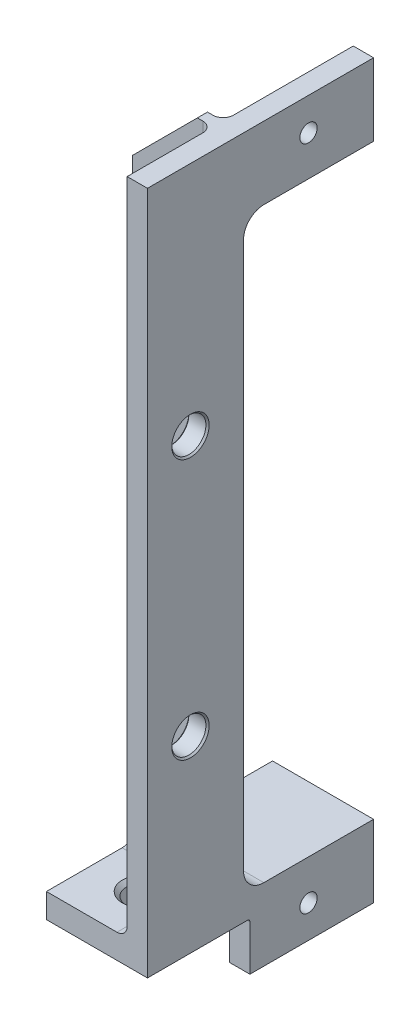
SolidWorks part; units mm, degrees
material "6061-T6 (SS)"
ref_plane "Front Plane" through (0, 0, 0) normal (0, 0, 1) x (1, 0, 0)
ref_plane "Top Plane" through (0, 0, 0) normal (0, 1, 0) x (1, 0, 0)
ref_plane "Right Plane" through (0, 0, 0) normal (1, 0, 0) x (0, 0, -1)
sketch "Sketch1" plane through (0, 0, 0) normal (1, 0, 0) x (0, 0, -1)
  line L0 (0, 0) -> (0, 23.4616) construction
  line L1 (7.5, 0) -> (-7.5, 0) construction
  line L2 (27.813, 57.15) -> (27.813, 45.848)
  line L3 (27.813, 45.848) -> (7.5, 45.848)
  line L4 (7.5, 45.848) -> (7.5, -45.848)
  line L5 (7.5, -45.848) -> (27.813, -45.848)
  line L6 (27.813, -45.848) -> (27.813, -57.15)
  line L7 (27.813, -57.15) -> (8.5, -57.15)
  line L8 (-7.5, -49.658) -> (-7.5, 57.15)
  line L9 (-7.5, 57.15) -> (27.813, 57.15)
  line L10 (8.5, -57.15) -> (8.5, -49.658)
  line L11 (8.5, -49.658) -> (-7.5, -49.658)
  point P15 (0, 0)
  point P16 (7.5, 0)
  dimension "D1" = 3.81
  dimension "D2" = 114.3
  dimension "D3" = 15
  dimension "D4" = 49.658
  dimension "D5" = 27.813
  dimension "D6" = 16
extrude "Boss-Extrude1" add sketch "Sketch1" along normal blind 3.175
sketch "Sketch2" plane through (0, 0, 0) normal (-1, 0, 0) x (0, 0, 1)
  line L0 (7.5, -49.658) -> (7.5, -45.848)
  line L1 (-27.813, -45.848) -> (-7.5, -45.848)
  line L2 (-27.813, -45.848) -> (-27.813, -49.658)
  line L3 (-27.813, -49.658) -> (7.5, -49.658)
  line L4 (7.5, -45.848) -> (-5.9125, -45.848)
  line L5 (7.5, 57.15) -> (7.5, -49.658) construction
  line L6 (-5.9125, 57.15) -> (-7.5, 57.15)
  line L7 (-27.813, 57.15) -> (7.5, 57.15) construction
  line L8 (-5.9125, -45.848) -> (-5.9125, 57.15)
  line L9 (-7.5, -45.848) -> (-7.5, 57.15)
  dimension "D1" = 1.5875
extrude "Boss-Extrude2" add sketch "Sketch2" along normal offset from surface (12.6073 mm away) 15.7823 up to face at (3.175, -9.9316, -12.8252)
sketch "Sketch3" plane through (0, -49.658, 0) normal (0, -1, 0) x (1, 0, 0)
  line L0 (0, 0) -> (-1.8044, 0) construction
  line L1 (3.175, 7.5) -> (3.175, -8.5) construction
  point P0 (-5.1079, 0)
  dimension "D1" = 8.2829
hole_wizard "#10 Clearance Hole1" positions "Sketch5" profile "Sketch4" hole size "#10" standard "Ansi Inch" end condition through all
sketch "Sketch5" plane through (0, -49.658, 0) normal (0, -1, 0) x (1, 0, 0)
  point P0 (-5.1079, 0)
sketch "Sketch4" plane through (-5.1079, -49.658, 0) normal (1, 0, 0) x (0, 0, -1)
  line L0 (0, 0) -> (0, 3.81)
  line L1 (0, 3.81) -> (3.1242, 3.81)
  line L2 (2.4892, 3.175) -> (2.4892, 0.635)
  line L3 (2.4892, 0.635) -> (3.1242, 0)
  line L5 (3.1242, 0) -> (0, 0)
  line L6 (-2.4892, 0.635) -> (-3.1242, 0) construction
  line L7 (3.1242, 3.81) -> (2.4892, 3.175)
  line L8 (-3.1242, 3.81) -> (-2.4892, 3.175) construction
  line L11 (0, -6.35) -> (0, 107.95) construction
  dimension "Thru Hole Dia." = 4.9784
  dimension "Thru Hole Depth" = 3.81
  dimension "Near C'Sink Dia." = 6.2484
  dimension "Near C'Sink Angle" = 90
  dimension "Far C'Sink Dia." = 6.2484
  dimension "Far C'Sink Angle" = 90
fillet "Fillet1" radius 1.5875 1 edges at (-6.3037, -45.848, -5.9125)
fillet "Fillet2" radius 3.175 2 edges at (-4.7162, -45.848, -7.5)
sketch "Sketch6" plane through (0, 0, -7.5) normal (0, 0, -1) x (-1, 0, 0)
  line L0 (2.4473, 57.15) -> (12.6073, 57.15)
  line L1 (12.6073, 57.15) -> (0, 57.15) construction
  line L2 (12.6073, 57.15) -> (12.6073, 46.99)
  line L3 (12.6073, -42.673) -> (12.6073, 57.15) construction
  line L4 (12.6073, 46.99) -> (2.4473, 57.15)
  dimension "D1" = 10.16
extrude "Cut-Extrude1" cut sketch "Sketch6" against normal through all
sketch "Sketch7" plane through (3.175, 0, 0) normal (1, 0, 0) x (0, 0, -1)
  line L3 (0, 0) -> (22.265, 0) construction
  line L4 (27.813, 45.848) -> (27.813, 57.15) construction
  point P3 (17.653, 52.07)
  dimension "D1" = 52.07
  dimension "D2" = 10.16
hole_wizard "#6-32 Tapped Hole1" positions "Sketch9" profile "Sketch8" tap size "#6-32" standard "Ansi Inch" end condition through all
sketch "Sketch9" plane through (3.175, 0, 0) normal (1, 0, 0) x (0, 0, -1)
  point P0 (17.653, 52.07)
sketch "Sketch8" plane through (3.175, 52.07, -17.653) normal (0, 1, 0) x (0, 0, -1)
  line L0 (0, 0) -> (0, 15.7823)
  line L1 (0, 15.7823) -> (1.3525, 15.7823)
  line L2 (1.3525, 15.7823) -> (1.3525, 0)
  line L5 (1.3525, 0) -> (0, 0)
  line L11 (0, -6.35) -> (0, 107.95) construction
  dimension "Thru Tap Drill Dia." = 2.7051
  dimension "Thru Tap Drill Depth" = 15.7823
cosmetic thread "Hole Thread1" parameters "D2"=3.5052
sketch "Sketch10" plane through (0, 0, 0) normal (-1, 0, 0) x (0, 0, 1)
  line L0 (0, 0) -> (22.4066, 0) construction
  line L1 (0, 0) -> (0, 9.2925) construction
  circle A0 centre (0.7874, 20.32) radius 2.667
  dimension "D1" = 5.334
  dimension "D2" = 20.32
  dimension "D3" = 0.7874
extrude "Cut-Extrude2" cut sketch "Sketch10" against normal through all
mirror "Mirror2" about plane through (0, 0, 0) normal (0, 1, 0) of "Cut-Extrude2"
chamfer "Chamfer1" distance 0.254 angle 45 4 edges at (3.175, -20.32, -1.8796) (3.175, 20.32, -1.8796) (0, 20.32, 3.4544) (0, -20.32, 3.4544)
fillet "Fillet3" radius 1.5875 5 edges at (0, -45.383, -5.4475)
mirror "Mirror1" about plane through (0, 0, 0) normal (0, 1, 0) of "#6-32 Tapped Hole1"
fillet "Fillet4" radius 0.3962 1 edges
